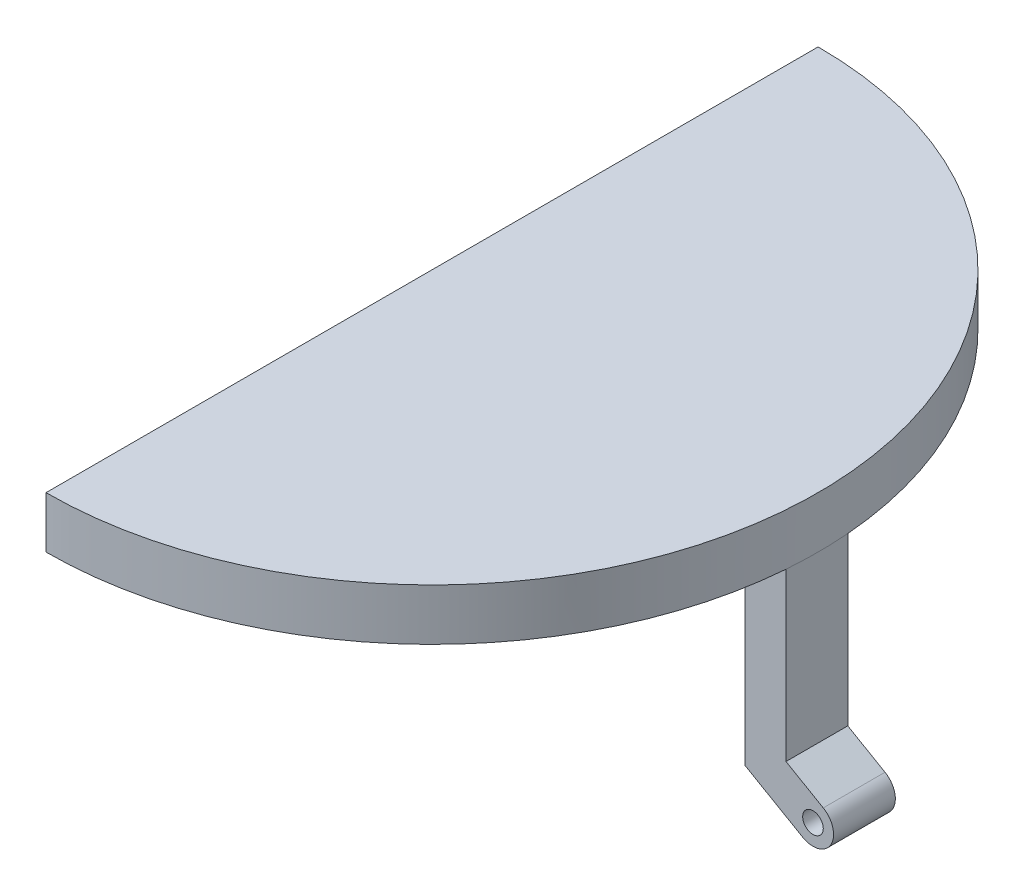
SolidWorks part; units mm, degrees
ref_plane "Ebene vorne" through (0, 0, 0) normal (0, 0, 1) x (1, 0, 0)
ref_plane "Ebene oben" through (0, 0, 0) normal (0, 1, 0) x (1, 0, 0)
ref_plane "Ebene rechts" through (0, 0, 0) normal (1, 0, 0) x (0, 0, -1)
sketch "Skizze1" plane through (0, 0, 0) normal (0, 1, 0) x (1, 0, 0)
  line L0 (0, 0) -> (0, -75)
  arc A0 (0, -75) -> (0, 0) centre (0, -37.5) ccw
  dimension "D1" = 75
extrude "Aufsatz-Linear austragen1" add sketch "Skizze1" along normal blind 5
sketch "Skizze10" plane through (0, 0, 0) normal (0, -1, 0) x (1, 0, 0)
  line L0 (37.3798, 40.5) -> (37.3798, 34.5)
  line L1 (0, 0) -> (0, 75) construction
  arc A0 (0, 0) -> (0, 75) centre (0, 37.5) ccw construction
  dimension "D1" = 6
ref_plane "Ebene1" through (37.3798, 0, 40.5) normal (0, 0, 1) x (1, 0, 0)
sketch "Skizze12" plane through (37.3798, 0, 40.5) normal (0, 0, 1) x (1, 0, 0)
  line L0 (0, 0) -> (0, -16.1778)
  line L2 (1.6202, -21.7321) -> (-4, -18.4872)
  line L3 (-4, 0) -> (0, 0)
  line L4 (-37.3798, 8.8878) -> (-37.3798, -28.7638) construction
  line L5 (2.6202, -15.4311) -> (2.6202, -25.351) construction
  line L6 (4.832, -20) -> (14.1192, -20) construction
  line L7 (-4, -18.4872) -> (-4, 0)
  line L8 (0, -16.1778) -> (3.6202, -18.2679)
  arc A0 (1.6202, -21.7321) -> (3.6202, -18.2679) centre (2.6202, -20) ccw
  dimension "D1" = 40
  dimension "D2" = 2
  dimension "D4" = 4
  dimension "D3" = 20
  dimension "D5" = 120
extrude "Aufsatz-Linear austragen2" add sketch "Skizze12" against normal up to vertex (6 mm away) contours L0 L8 A0 L2 L7 L3 up to point (37.3798, 0, 34.5)
sketch "Skizze13" plane through (37.3798, 0, 40.5) normal (0, 0, 1) x (1, 0, 0)
  circle A4 centre (2.6202, -20) radius 1
  arc A5 (1.6202, -21.7321) -> (3.6202, -18.2679) centre (2.6202, -20) ccw construction
extrude "Schnitt-Linear austragen1" cut sketch "Skizze13" against normal up to surface (6 mm away) up to face at (37.2085, -12.6108, 34.5)
